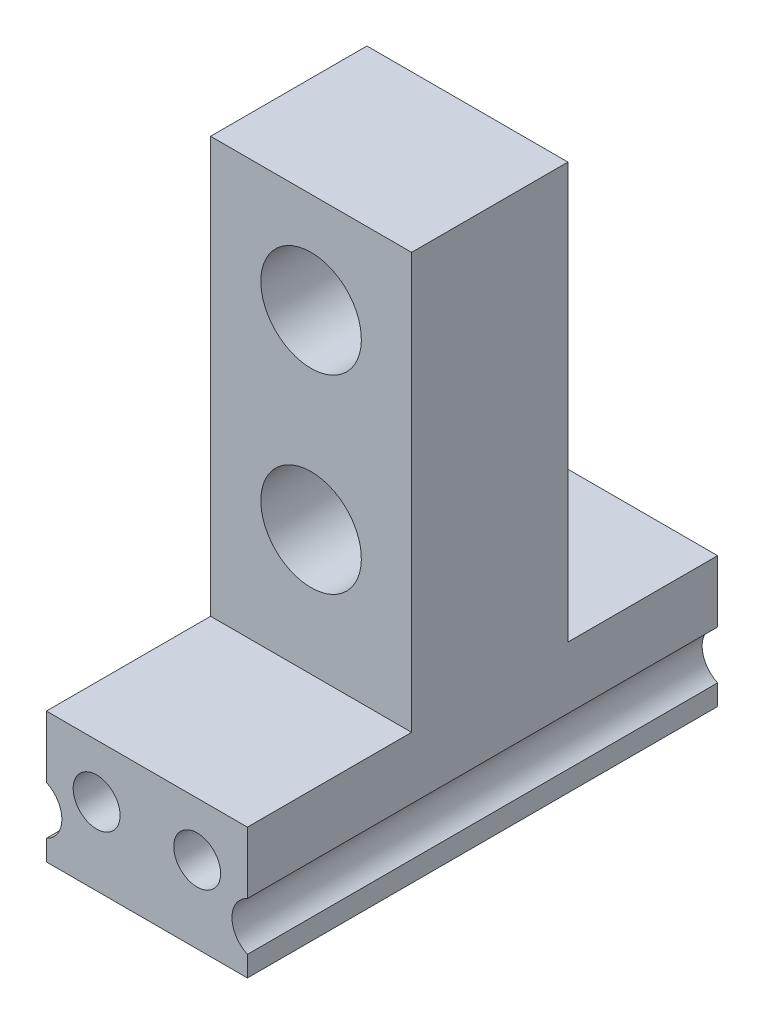
SolidWorks part; units mm, degrees
ref_plane "前视基准面" through (0, 0, 0) normal (0, 0, 1) x (1, 0, 0)
ref_plane "上视基准面" through (0, 0, 0) normal (0, 1, 0) x (1, 0, 0)
ref_plane "右视基准面" through (0, 0, 0) normal (1, 0, 0) x (0, 0, -1)
sketch "草图6" plane through (0, 0, 0) normal (0, 0, 1) x (1, 0, 0)
  line L337 (415.0997, 796.1132) -> (415.0997, 758.8932)
  line L338 (433.0997, 796.1132) -> (433.0997, 758.8932)
  line L339 (415.0997, 796.1132) -> (433.0997, 796.1132)
  line L340 (415.0997, 758.8932) -> (433.0997, 758.8932)
  line L341 (415.0997, 758.8932) -> (415.0997, 753.3584)
  line L342 (415.0997, 749.028) -> (415.0997, 747.1932)
  line L343 (415.0997, 747.1932) -> (433.0997, 747.1932)
  line L344 (433.0997, 747.1932) -> (433.0997, 749.028)
  line L345 (433.0997, 753.3584) -> (433.0997, 758.8932)
  circle A53 centre (424.0997, 770.1132) radius 4
  circle A54 centre (424.0997, 787.1132) radius 4
  circle A55 centre (419.5997, 754.0932) radius 1.5
  circle A56 centre (428.5997, 754.0932) radius 1.5
  arc A57 (415.0997, 749.028) -> (415.0997, 753.3584) centre (414.0997, 751.1932) ccw
  arc A58 (433.0997, 753.3584) -> (433.0997, 749.028) centre (434.0997, 751.1932) ccw
  circle A59 centre (419.5997, 754.0932) radius 2.1
  circle A60 centre (424.0997, 787.1132) radius 4.5
  circle A61 centre (424.0997, 770.1132) radius 4.5
  circle A62 centre (428.5997, 754.0932) radius 2.1
  dimension "D3" = 8
  dimension "D5" = 9
  dimension "D1" = 18
  dimension "D2" = 37.22
  dimension "D4" = 11.7
  dimension "D6" = 17
  dimension "D7" = 9
extrude "凸台-拉伸2" add sketch "草图6" along normal blind 42.1 contours L337 L340 L338 L339 A61 A60 | A58 L345 L340 L341 A57 L342 L343 L344 A62 A59 | A54 | A53
sketch "草图8" plane through (433.0997, 0, 0) normal (1, 0, 0) x (0, 0, -1)
  line L0 (-42.1, 796.1132) -> (0, 796.1132) construction
  line L1 (-42.1, 796.1132) -> (-27.4, 796.1132)
  line L2 (-42.1, 796.1132) -> (-42.1, 758.8932)
  line L3 (-42.1, 758.8932) -> (-27.4, 758.8932)
  line L4 (-27.4, 796.1132) -> (-27.4, 758.8932)
  line L5 (0, 796.1132) -> (0, 753.3584) construction
  line L6 (-13.4, 796.1132) -> (0, 796.1132)
  line L7 (-13.4, 796.1132) -> (-13.4, 758.8932)
  line L8 (-13.4, 758.8932) -> (0, 758.8932)
  line L9 (0, 796.1132) -> (0, 758.8932)
  line L10 (-42.1, 796.1132) -> (-42.1, 753.3584) construction
  dimension "D1" = 0
  dimension "D2" = 14.7
  dimension "D3" = 13.4
  dimension "D4" = 37.22
  dimension "D5" = 37.22
extrude "切除-拉伸1" cut sketch "草图8" against normal blind 42.1
